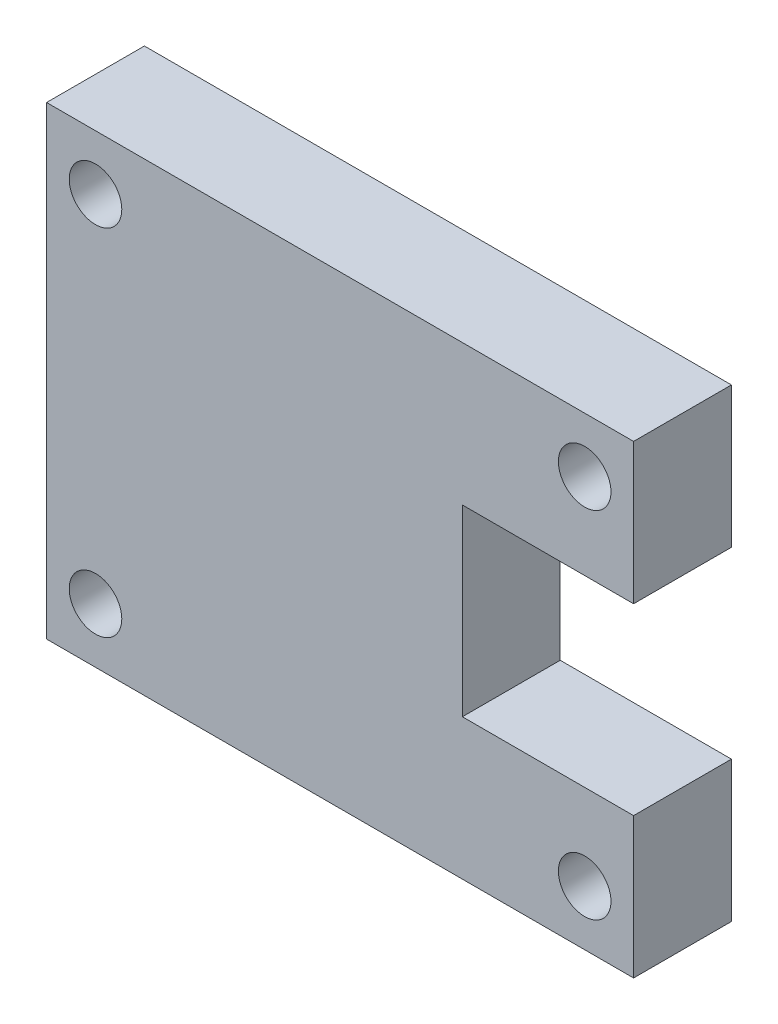
SolidWorks part; units mm, degrees
material "Alliage 1060"
ref_plane "Plan de face" through (0, 0, 0) normal (0, 0, 1) x (1, 0, 0)
ref_plane "Plan de dessus" through (0, 0, 0) normal (0, 1, 0) x (1, 0, 0)
ref_plane "Plan de droite" through (0, 0, 0) normal (1, 0, 0) x (0, 0, -1)
sketch "Esquisse1" plane through (0, 0, 0) normal (0, 0, 1) x (1, 0, 0)
  line L1 (-24, -19) -> (24, -19)
  line L2 (-24, -19) -> (-24, 19)
  line L3 (-24, 19) -> (24, 19)
  line L4 (24, -19) -> (24, 19)
  line L5 (-24, -19) -> (24, 19) construction
  line L6 (-24, 19) -> (24, -19) construction
  point P0 (0, 0)
  dimension "D1" = 48
  dimension "D2" = 38
extrude "Boss.-Extru.1" add sketch "Esquisse1" along normal blind 8
sketch "Esquisse2" plane through (0, 0, 8) normal (0, 0, 1) x (1, 0, 0)
  line L0 (24, -19) -> (24, 19) construction
  line L1 (22.5, 14.5) -> (24, 14.5) construction
  line L2 (20, 17) -> (20, 19) construction
  line L3 (24, 19) -> (-24, 19) construction
  line L4 (0, 19) -> (0, -19) construction
  line L5 (-24, -19) -> (24, -19) construction
  line L6 (-24, 0) -> (24, 0) construction
  line L7 (-24, 19) -> (-24, -19) construction
  circle A0 centre (20, 14.5) radius 2.5
  circle A2 centre (-20, 14.5) radius 2.5
  circle A3 centre (20, -14.5) radius 2.5
  circle A4 centre (-20, -14.5) radius 2.5
  dimension "D3" = 40
  dimension "D1" = 1.5
  dimension "D2" = 2
sketch "Esquisse4" plane through (0, 0, 8) normal (0, 0, 1) x (1, 0, 0)
  line L0 (24, 7.5) -> (10, 7.5)
  line L1 (24, -19) -> (24, 19) construction
  line L2 (10, 7.5) -> (10, -7.5)
  line L3 (10, -7.5) -> (24, -7.5)
  line L4 (24, 7.5) -> (24, 19)
  line L5 (24, -7.5) -> (24, -19)
  line L6 (24, 7.5) -> (24, -7.5)
  line M10 (24, -19) -> (24, 19)
  dimension "D1" = 15
  dimension "D2" = 14
extrude "Enlèv. mat.-Extru.2" cut sketch "Esquisse4" against normal blind 8 contours L2 L3 L0 M10
hole_wizard "Dégagement M41" positions "Esquisse3D1" profile "Esquisse5" hole size "M4" standard "ISO"
sketch3d "Esquisse3D1"
  point P0 (-20, 14.5, 8)
  point P3 (20, 14.5, 8)
  point P6 (-20, -14.5, 8)
  point P9 (20, -14.5, 8)
sketch "Esquisse5" plane through (-20, 14.5, 8) normal (1, 0, 0) x (0, -1, 0)
  line L0 (0, 0) -> (0, 11.2919)
  line L1 (0, 11.2919) -> (2.15, 10)
  line L2 (2.15, 10) -> (2.15, 0)
  line L5 (2.15, 0) -> (0, 0)
  line L10 (0, 11.2919) -> (-2.15, 10) construction
  line L11 (0, -6.35) -> (0, 107.95) construction
  dimension "Diamètre du perçage" = 4.3
  dimension "Profondeur du perçage" = 10
  dimension "Angle de pointe" = 118
